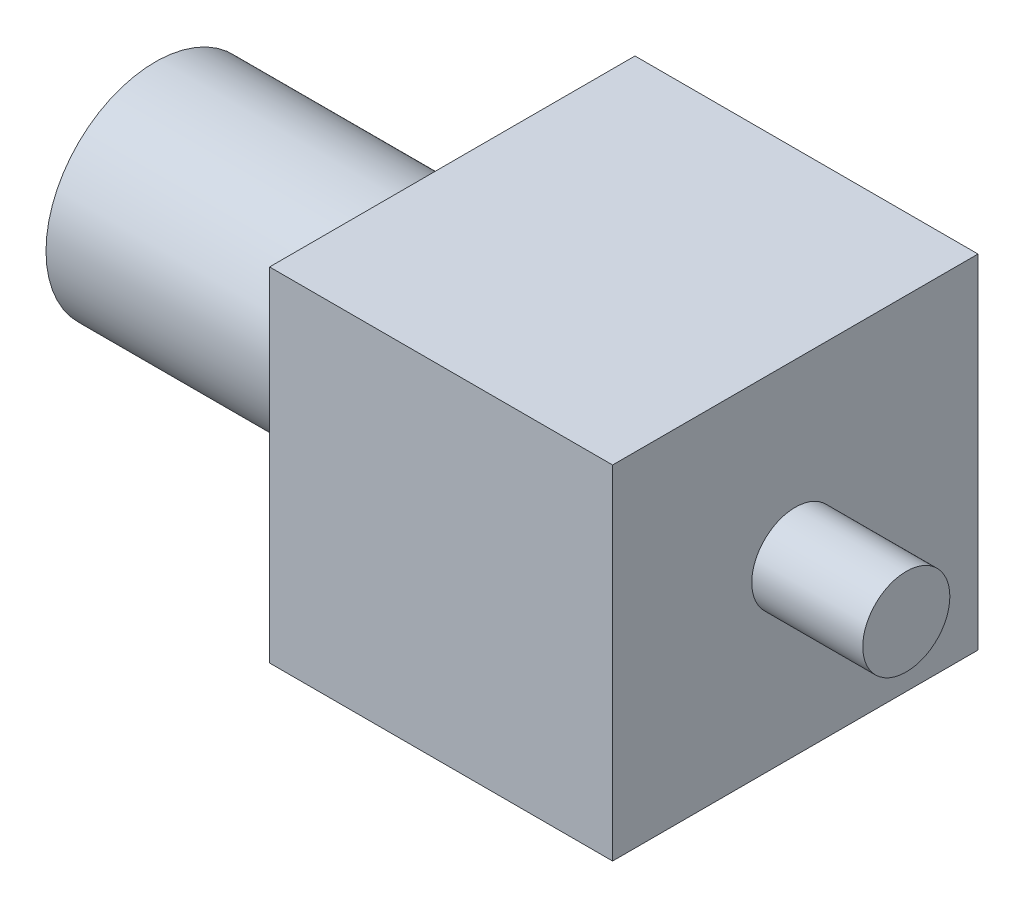
SolidWorks part; units mm, degrees
ref_plane "Front Plane" through (0, 0, 0) normal (0, 0, 1) x (1, 0, 0)
ref_plane "Top Plane" through (0, 0, 0) normal (0, 1, 0) x (1, 0, 0)
ref_plane "Right Plane" through (0, 0, 0) normal (1, 0, 0) x (0, 0, -1)
sketch "Sketch1" plane through (0, 0, 0) normal (0, 0, 1) x (1, 0, 0)
  line L1 (0, 0) -> (25, 0)
  line L2 (0, 0) -> (0, 25)
  line L3 (0, 25) -> (25, 25)
  line L4 (25, 0) -> (25, 25)
  dimension "D1" = 25
  dimension "D2" = 25
extrude "Boss-Extrude1" add sketch "Sketch1" along normal blind 26.6319
sketch "Sketch2" plane through (0, 0, 0) normal (-1, 0, 0) x (0, 0, 1)
  line L0 (13.3159, 25) -> (13.316, 0) construction
  line L1 (26.6319, 25) -> (0, 25) construction
  line L2 (26.6319, 0) -> (0, 0) construction
  line L3 (0, 12.5) -> (26.6319, 12.5) construction
  line L4 (0, 25) -> (0, 0) construction
  line L5 (26.6319, 25) -> (26.6319, 0) construction
  circle A0 centre (13.3159, 12.5) radius 7.9693
  dimension "D1" = 15.9385
extrude "Boss-Extrude2" add sketch "Sketch2" along normal blind 21.6408
sketch "Sketch3" plane through (25, 0, 0) normal (1, 0, 0) x (0, 0, -1)
  line L0 (-26.6319, 25) -> (-13.316, 25) construction
  line L1 (-26.6319, 25) -> (0, 25) construction
  line L2 (-26.6319, 12.5) -> (-13.316, 12.5) construction
  line L3 (-26.6319, 0) -> (-26.6319, 25) construction
  circle A0 centre (-13.316, 12.5) radius 3.175
extrude "Boss-Extrude3" add sketch "Sketch3" along normal blind 8.0899
